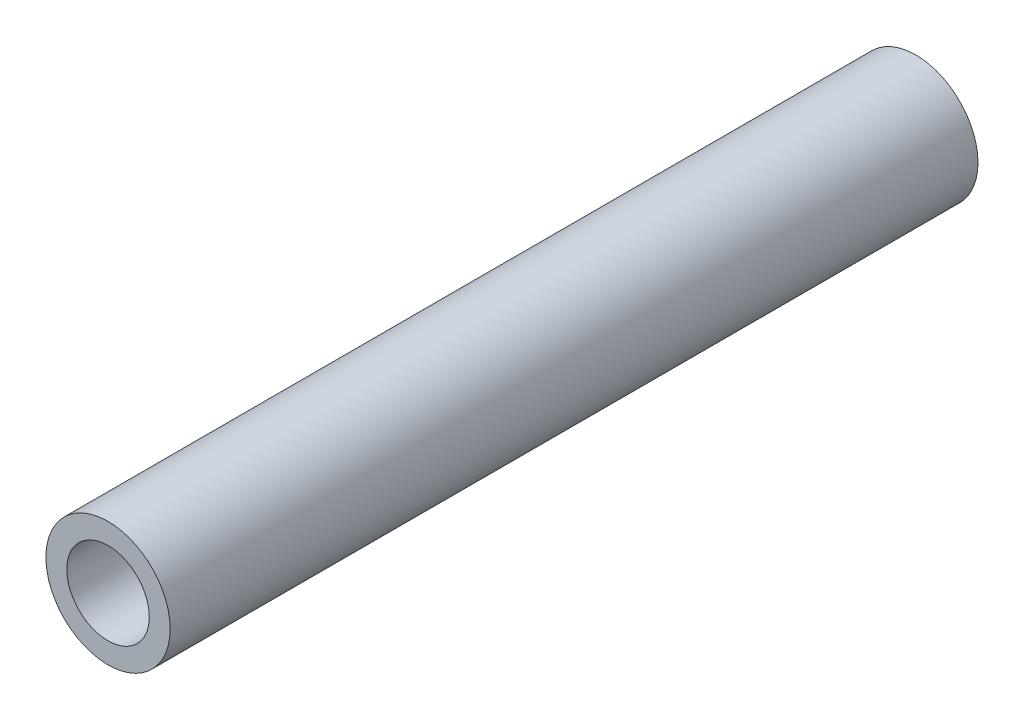
SolidWorks part; units mm, degrees
material "6061-T6 (SS)"
ref_plane "Front Plane" through (0, 0, 0) normal (0, 0, 1) x (1, 0, 0)
ref_plane "Top Plane" through (0, 0, 0) normal (0, 1, 0) x (1, 0, 0)
ref_plane "Right Plane" through (0, 0, 0) normal (1, 0, 0) x (0, 0, -1)
sketch "Sketch1" plane through (0, 0, 0) normal (0, 0, 1) x (1, 0, 0)
  circle A0 centre (0, 0) radius 3.175
  circle A1 centre (0, 0) radius 2.1082
  dimension "D1" = 1.0668
  dimension "D2" = 6.35
extrude "Boss-Extrude1" add sketch "Sketch1" against normal blind 41.275
chamfer "Chamfer1" distance 0.254 angle 45 1 edges at (2.1082, 0, -41.275)
